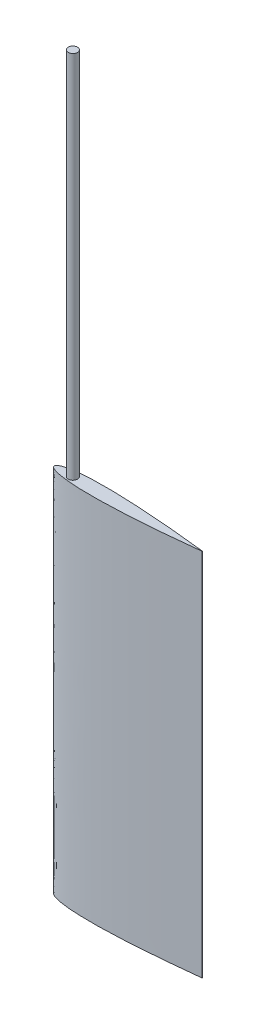
SolidWorks part; units mm, degrees
ref_plane "Front Plane" through (0, 0, 0) normal (0, 0, 1) x (1, 0, 0)
ref_plane "Top Plane" through (0, 0, 0) normal (0, 1, 0) x (1, 0, 0)
ref_plane "Right Plane" through (0, 0, 0) normal (1, 0, 0) x (0, 0, -1)
sketch "Sketch1" plane through (0, 0, 0) normal (0, 1, 0) x (1, 0, 0)
  line L0 (0, 0) -> (151.6412, 0) construction
  line L1 (50.8, 0.0508) -> (50.8, 0)
  line L2 (50.8, 0) -> (0, 0)
  spline S0 degree 4 poles (0, 0) (0, 0.0399) (0.0058, 0.1002) (0.0259, 0.1818) (0.0698, 0.2802) (0.1206, 0.3641) (0.1925, 0.4566) (0.298, 0.564) (0.4615, 0.696) (0.73, 0.8662) (1.19, 1.0893) (2.0141, 1.3842) (3.4677, 1.7459) (5.805, 2.1191) (8.9329, 2.3992) (12.6558, 2.545) (16.6831, 2.5549) (20.7073, 2.4604) (24.7317, 2.2876) (28.2456, 2.0848) (31.2631, 1.8805) (33.7647, 1.6943) (35.7854, 1.5334) (38.2649, 1.3262) (40.8226, 1.0951) (43.2452, 0.8652) (45.8658, 0.597) (47.6685, 0.4072) (50.1921, 0.1236) (51.6149, -0.0438) (53.6676, -0.2942) (54.6699, -0.4256) (55.4746, -0.5287) (55.6782, -0.5575) (55.8908, -0.585) knots 0 0 0 0 0 0.002798 0.004281 0.005885 0.007584 0.009711 0.012533 0.016488 0.022392 0.032104 0.048557 0.078181 0.127994 0.199053 0.270111 0.34117 0.412229 0.483288 0.554347 0.589876 0.625406 0.660935 0.696465 0.767523 0.803053 0.838582 0.874112 0.909641 0.954821 0.97741 0.988705 1 1 1 1 1 construction
  spline S1 degree 4 poles (0, 0) (0, 0.0399) (0.0058, 0.1002) (0.0259, 0.1818) (0.0698, 0.2802) (0.1206, 0.3641) (0.1925, 0.4566) (0.298, 0.564) (0.4615, 0.696) (0.73, 0.8662) (1.19, 1.0893) (2.0141, 1.3842) (3.4677, 1.7459) (5.805, 2.1191) (8.9329, 2.3992) (12.6558, 2.545) (16.6831, 2.5549) (20.7073, 2.4604) (24.7317, 2.2876) (28.2456, 2.0848) (31.2631, 1.8805) (33.7647, 1.6943) (35.7854, 1.5334) (38.2649, 1.3262) (40.8226, 1.0951) (43.2452, 0.8652) (45.8658, 0.597) (47.6685, 0.4072) (49.4409, 0.208) (50.3453, 0.104) (50.8, 0.0508) knots 0 0 0 0 0 0.002798 0.004281 0.005885 0.007584 0.009711 0.012533 0.016488 0.022392 0.032104 0.048557 0.078181 0.127994 0.199053 0.270111 0.34117 0.412229 0.483288 0.554347 0.589876 0.625406 0.660935 0.696465 0.767523 0.803053 0.838582 0.874112 0.909641 0.909641 0.909641 0.909641 0.909641
extrude "Boss-Extrude1" add sketch "Sketch1" along normal blind 127
mirror "Mirror1" about plane through (50.8, 127, 0) normal (0, 0, -1) of bodies 101
sketch "Sketch2" plane through (0, 127, 0) normal (0, 1, 0) x (1, 0, 0)
  line L0 (0, 0) -> (6.35, 0) construction
  circle A0 centre (6.35, 0) radius 1.5875
  dimension "D2" = 3.175
  dimension "D1" = 6.35
extrude "Boss-Extrude2" add sketch "Sketch2" along normal blind 127
